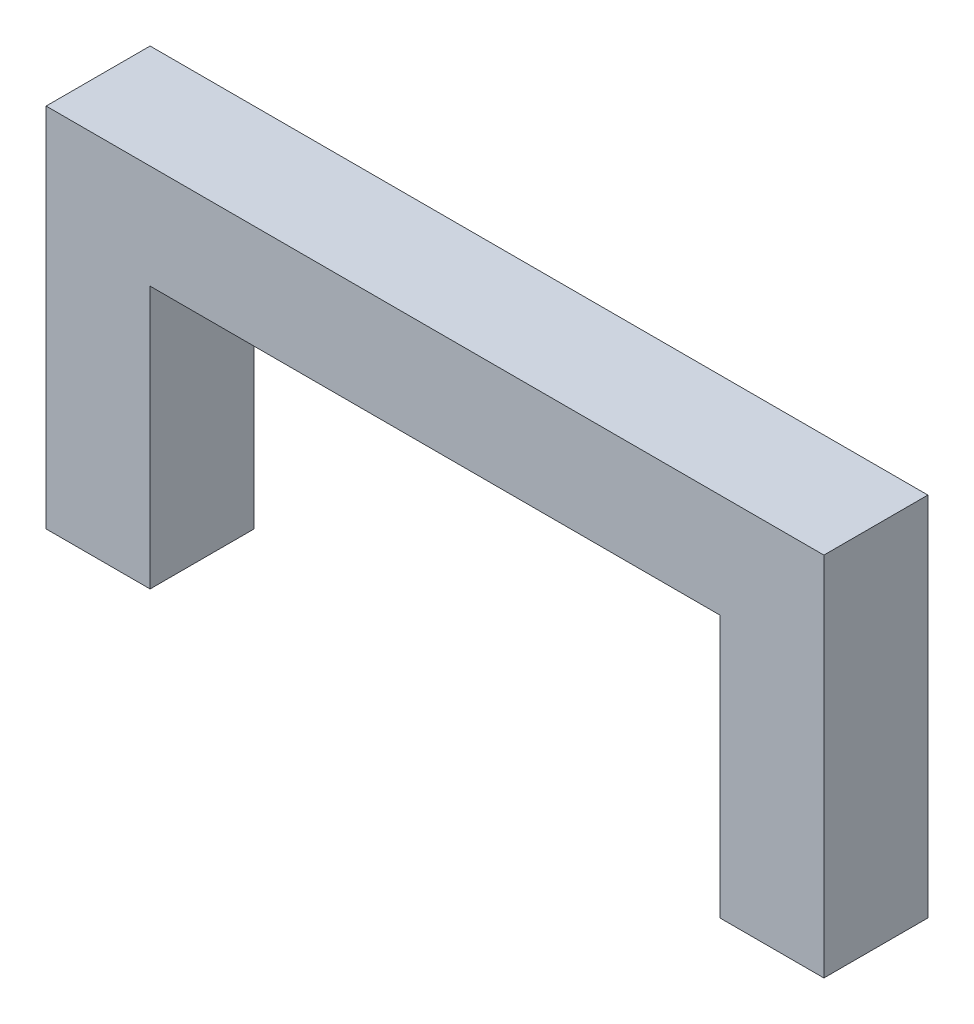
SolidWorks part; units mm, degrees
ref_plane "Front Plane" through (0, 0, 0) normal (0, 0, 1) x (1, 0, 0)
ref_plane "Top Plane" through (0, 0, 0) normal (0, 1, 0) x (1, 0, 0)
ref_plane "Right Plane" through (0, 0, 0) normal (1, 0, 0) x (0, 0, -1)
sketch "Sketch2" plane through (0, 0, 0) normal (0, 1, 0) x (1, 0, 0)
  line L0 (0, -19.05) -> (142.49, -19.05) construction
  line L1 (0, 0) -> (19.05, 0)
  line L2 (0, 0) -> (0, -19.05)
  line L3 (0, -19.05) -> (19.05, -19.05)
  line L4 (19.05, 0) -> (19.05, -19.05)
  line L6 (142.49, -19.05) -> (123.44, -19.05)
  line L7 (142.49, -19.05) -> (142.49, 0)
  line L8 (142.49, 0) -> (123.44, 0)
  line L9 (123.44, -19.05) -> (123.44, 0)
  dimension "D1" = 19.05
  dimension "D2" = 19.05
  dimension "D3" = 19.05
  dimension "D4" = 142.49
  dimension "D5" = 19.05
extrude "Boss-Extrude1" add sketch "Sketch2" along normal blind 48.05
sketch "Sketch3" plane through (0, 48.05, 0) normal (0, 1, 0) x (1, 0, 0)
  line L1 (0, 0) -> (142.49, 0)
  line L2 (0, 0) -> (0, -19.05)
  line L3 (0, -19.05) -> (142.49, -19.05)
  line L4 (142.49, 0) -> (142.49, -19.05)
extrude "Boss-Extrude2" add sketch "Sketch3" along normal blind 19.05
